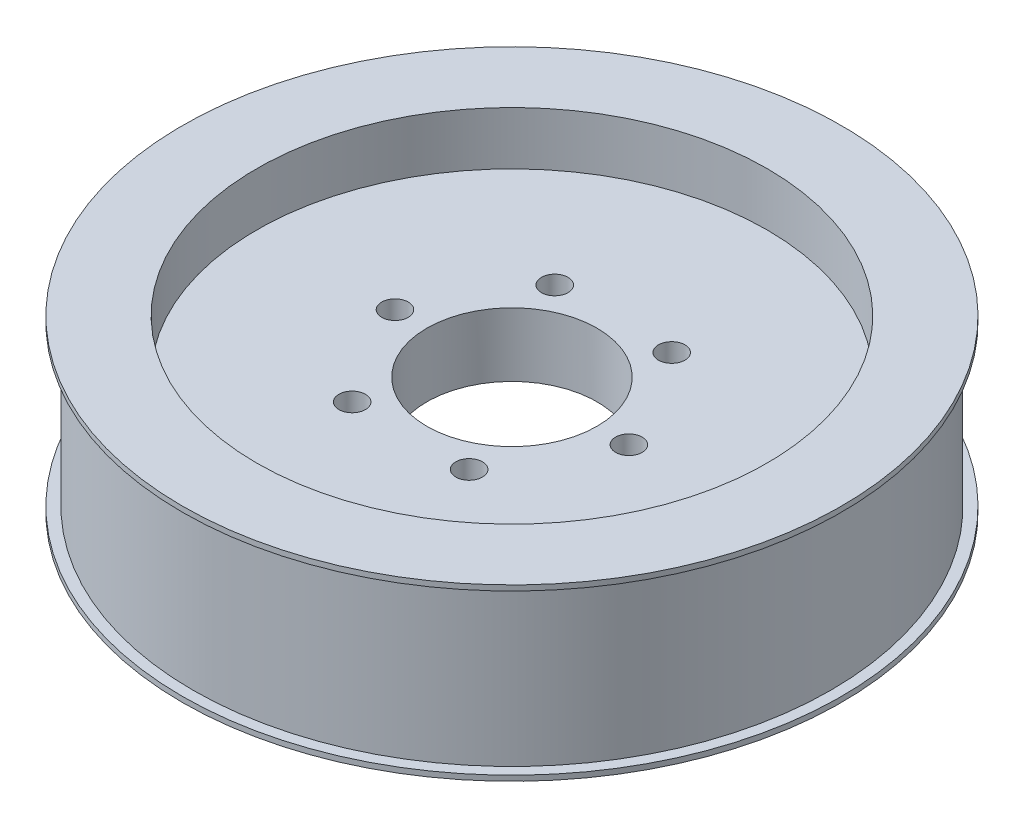
SolidWorks part; units mm, degrees
ref_plane "Front Plane" through (0, 0, 0) normal (0, 0, 1) x (1, 0, 0)
ref_plane "Top Plane" through (0, 0, 0) normal (0, 1, 0) x (1, 0, 0)
ref_plane "Right Plane" through (0, 0, 0) normal (1, 0, 0) x (0, 0, -1)
sketch "Sketch1" plane through (0, 0, 0) normal (0, 0, 1) x (1, 0, 0)
  line L0 (0, 36.0129) -> (0, -30.7112) construction
  line L1 (0, 10.1509) -> (24, 10.1509)
  line L2 (24, 10.1509) -> (24, 15.1509)
  line L3 (24, 15.1509) -> (31, 15.1509)
  line L4 (31, 15.1509) -> (31, 14.6509)
  line L5 (31, 14.6509) -> (30, 14.6509)
  line L6 (30, 14.6509) -> (30, -0.3491)
  line L7 (0, 10.1509) -> (0, 4.1509)
  line L8 (31, -0.3491) -> (30, -0.3491)
  line L9 (31, -0.8491) -> (31, -0.3491)
  line L10 (24, -0.8491) -> (31, -0.8491)
  line L11 (24, 4.1509) -> (24, -0.8491)
  line L12 (0, 4.1509) -> (24, 4.1509)
  dimension "D1" = 60
  dimension "D2" = 1
  dimension "D3" = 0.5
  dimension "D4" = 6
  dimension "D7" = 15
revolve "Revolve1" add sketch "Sketch1" angle 360 about L0
sketch "Sketch2" plane through (0, 10.1509, 0) normal (0, 1, 0) x (1, 0, 0)
  circle A0 centre (0, 0) radius 11 construction
  circle A1 centre (0, 0) radius 8
  circle A2 centre (11, 0) radius 1.25
  circle A3 centre (5.5, -9.5263) radius 1.25
  circle A4 centre (-5.5, -9.5263) radius 1.25
  circle A5 centre (-11, 0) radius 1.25
  circle A6 centre (-5.5, 9.5263) radius 1.25
  circle A7 centre (5.5, 9.5263) radius 1.25
  point P18 (0, 0)
  dimension "D1" = 22
  dimension "D2" = 16
  dimension "D3" = 2.5
  dimension "D4" = 6
extrude "Cut-Extrude1" cut sketch "Sketch2" against normal mid plane 30
